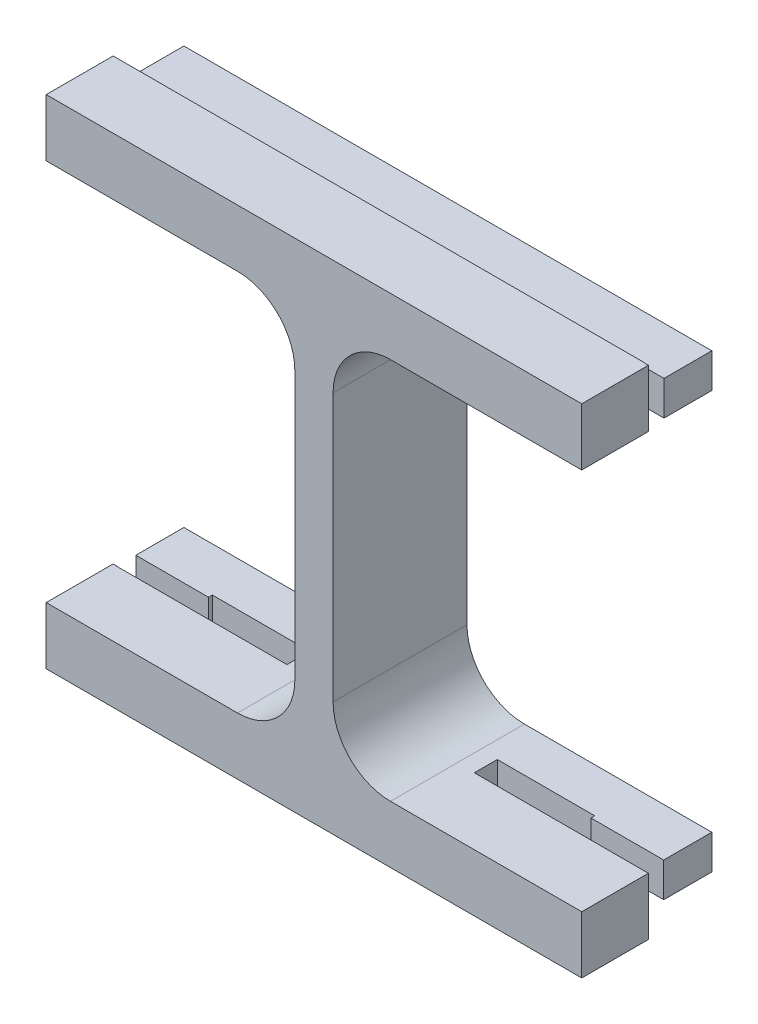
SolidWorks part; units mm, degrees
ref_plane "Ön Düzlem" through (0, 0, 0) normal (0, 0, 1) x (1, 0, 0)
ref_plane "Üst Düzlem" through (0, 0, 0) normal (0, 1, 0) x (1, 0, 0)
ref_plane "Sağ Düzlem" through (0, 0, 0) normal (1, 0, 0) x (0, 0, -1)
sketch "Sketch1" plane through (0, 0, 0) normal (0, 0, 1) x (1, 0, 0)
  line L1 (-13.4459, 11.7857) -> (16.5541, 11.7857)
  line L2 (-13.4459, 11.7857) -> (-13.4459, -10.2143)
  line L3 (-13.4459, -10.2143) -> (16.5541, -10.2143)
  line L4 (16.5541, 11.7857) -> (16.5541, -10.2143)
  dimension "D1" = 30
  dimension "D2" = 22
extrude "Boss-Extrude1" add sketch "Sketch1" along normal blind 2
sketch "Sketch2" plane through (0, 0, 2) normal (0, 0, 1) x (1, 0, 0)
  line L0 (-13.4459, -10.2143) -> (16.5541, -10.2143) construction
  line L1 (-12.4459, 10.7857) -> (0.5541, 10.7857)
  line L2 (-12.4459, 10.7857) -> (-12.4459, -9.2143)
  line L3 (-12.4459, -9.2143) -> (0.5541, -9.2143)
  line L4 (0.5541, 10.7857) -> (0.5541, -9.2143)
  line L5 (-13.4459, 11.7857) -> (-13.4459, -10.2143) construction
  line L6 (16.5541, -10.2143) -> (16.5541, 11.7857) construction
  line L7 (15.5541, 10.7857) -> (2.5541, 10.7857)
  line L8 (15.5541, 10.7857) -> (15.5541, -9.2143)
  line L9 (15.5541, -9.2143) -> (2.5541, -9.2143)
  line L10 (2.5541, 10.7857) -> (2.5541, -9.2143)
  dimension "D1" = 20
  dimension "D2" = 13
  dimension "D3" = 1
  dimension "D4" = 1
  dimension "D5" = 13
  dimension "D6" = 1
extrude "Cut-Extrude1" cut sketch "Sketch2" against normal blind 2
fillet "Fillet1" radius 3 8 edges at (15.5541, 10.7857, 1) (15.5541, -9.2143, 1) (2.5541, 10.7857, 1) (2.5541, -9.2143, 1) (0.5541, -9.2143, 1) (-12.4459, 10.7857, 1) (-12.4459, -9.2143, 1) (0.5541, 10.7857, 1)
sketch "Sketch3" plane through (0, 0, 0) normal (0, 0, -1) x (-1, 0, 0)
  line L1 (-16.5541, -10.2143) -> (13.4459, -10.2143)
  line L2 (-16.5541, -10.2143) -> (-16.5541, 11.7857)
  line L3 (-16.5541, 11.7857) -> (13.4459, 11.7857)
  line L4 (13.4459, -10.2143) -> (13.4459, 11.7857)
extrude "Boss-Extrude2" add sketch "Sketch3" along normal blind 20
sketch "Sketch4" plane through (0, 11.7857, 0) normal (0, 1, 0) x (1, 0, 0)
  line L1 (-13.4459, -2) -> (16.5541, -2)
  line L2 (-13.4459, -2) -> (-13.4459, 20)
  line L3 (-13.4459, 20) -> (16.5541, 20)
  line L4 (16.5541, -2) -> (16.5541, 20)
extrude "Boss-Extrude3" add sketch "Sketch4" along normal blind 2
sketch "Sketch5" plane through (0, -10.2143, 0) normal (0, -1, 0) x (-1, 0, 0)
  line L1 (-16.5541, -2) -> (13.4459, -2)
  line L2 (-16.5541, -2) -> (-16.5541, 20)
  line L3 (-16.5541, 20) -> (13.4459, 20)
  line L4 (13.4459, -2) -> (13.4459, 20)
extrude "Boss-Extrude4" add sketch "Sketch5" along normal blind 2
sketch "Sketch6" plane through (16.5541, 0, 0) normal (1, 0, 0) x (0, 0, -1)
  line L0 (20, -12.2143) -> (-2, -12.2143) construction
  line L1 (20, 13.7857) -> (1.9849, 13.7857)
  line L2 (20, 13.7857) -> (20, -12.2143)
  line L3 (20, -12.2143) -> (1.9849, -12.2143)
  line L4 (1.9849, 13.7857) -> (1.9849, -12.2143)
extrude "Cut-Extrude2" cut sketch "Sketch6" against normal blind 1.2
sketch "Sketch7" plane through (-13.4459, 0, 0) normal (-1, 0, 0) x (0, 0, 1)
  line L0 (2, -12.2143) -> (-20, -12.2143) construction
  line L1 (-20, 13.7857) -> (-2, 13.7857)
  line L2 (-20, 13.7857) -> (-20, -12.2143)
  line L3 (-20, -12.2143) -> (-2, -12.2143)
  line L4 (-2, 13.7857) -> (-2, -12.2143)
  dimension "D1" = 4
extrude "Cut-Extrude3" cut sketch "Sketch7" against normal blind 1.2
sketch "Sketch8" plane through (0, 13.7857, 0) normal (0, 1, 0) x (1, 0, 0)
  line L1 (-12.2459, 2) -> (15.3541, 2)
  line L2 (-12.2459, 2) -> (-12.2459, 20)
  line L3 (-12.2459, 20) -> (15.3541, 20)
  line L4 (15.3541, 2) -> (15.3541, 20)
extrude "Cut-Extrude4" cut sketch "Sketch8" against normal blind 1.2
sketch "Sketch9" plane through (0, -12.2143, 0) normal (0, -1, 0) x (1, 0, 0)
  line L1 (15.3541, -1.9849) -> (-12.2459, -1.9849)
  line L2 (15.3541, -1.9849) -> (15.3541, -20)
  line L3 (15.3541, -20) -> (-12.2459, -20)
  line L4 (-12.2459, -1.9849) -> (-12.2459, -20)
extrude "Cut-Extrude5" cut sketch "Sketch9" against normal blind 1.2
sketch "Sketch10" plane through (0, 12.5857, 0) normal (0, 1, 0) x (1, 0, 0)
  line L0 (-2.4459, -2) -> (-9.4459, -2) construction
  line L1 (-12.2459, 2) -> (-3.3459, 2)
  line L2 (-12.2459, 2) -> (-12.2459, 3)
  line L3 (-12.2459, 3) -> (-3.3459, 3)
  line L4 (-3.3459, 2) -> (-3.3459, 3)
  line L5 (15.3541, 2) -> (6.4541, 2)
  line L6 (15.3541, 2) -> (15.3541, 3)
  line L7 (15.3541, 3) -> (6.4541, 3)
  line L8 (6.4541, 2) -> (6.4541, 3)
  line L9 (12.5541, -2) -> (5.5541, -2) construction
  point P10 (-5.9459, -2)
  point P13 (-5.9459, -2)
  point P14 (9.0541, -2)
  dimension "D1" = 1
  dimension "D2" = 2.6
  dimension "D3" = 2.6
extrude "Cut-Extrude7" cut sketch "Sketch10" against normal up to surface (1.8 mm away) up to face at (-5.9459, 10.7857, 1)
sketch "Sketch12" plane through (0, 12.5857, 0) normal (0, 1, 0) x (1, 0, 0)
  line L1 (-3.3459, 2) -> (-8.5459, 2)
  line L2 (-3.3459, 2) -> (-3.3459, 3.2)
  line L3 (-3.3459, 3.2) -> (-8.5459, 3.2)
  line L4 (-8.5459, 2) -> (-8.5459, 3.2)
  line L5 (6.4541, 2) -> (11.6541, 2)
  line L6 (6.4541, 2) -> (6.4541, 3.2)
  line L7 (6.4541, 3.2) -> (11.6541, 3.2)
  line L8 (11.6541, 2) -> (11.6541, 3.2)
  dimension "D1" = 5.2
  dimension "D2" = 1.2
  dimension "D3" = 5.2
extrude "Cut-Extrude8" cut sketch "Sketch12" against normal up to surface (1.8 mm away) up to face at (-7.7959, 10.7857, -2.5)
sketch "Sketch13" plane through (0, 0, 0) normal (0, 0, 1) x (1, 0, 0)
  line L0 (-9.4459, 10.7857) -> (-2.4459, 10.7857)
  line L1 (-12.4459, 7.7857) -> (-12.4459, -6.2143)
  line L2 (-9.4459, -9.2143) -> (-2.4459, -9.2143)
  line L3 (0.5541, -6.2143) -> (0.5541, 7.7857)
  line L4 (5.5541, 10.7857) -> (12.5541, 10.7857)
  line L5 (2.5541, 7.7857) -> (2.5541, -6.2143)
  line L6 (5.5541, -9.2143) -> (12.5541, -9.2143)
  line L7 (15.5541, -6.2143) -> (15.5541, 7.7857)
  arc A0 (-9.4459, 10.7857) -> (-12.4459, 7.7857) centre (-9.4459, 7.7857) ccw
  arc A1 (-12.4459, -6.2143) -> (-9.4459, -9.2143) centre (-9.4459, -6.2143) ccw
  arc A2 (-2.4459, -9.2143) -> (0.5541, -6.2143) centre (-2.4459, -6.2143) ccw
  arc A3 (0.5541, 7.7857) -> (-2.4459, 10.7857) centre (-2.4459, 7.7857) ccw
  arc A4 (5.5541, 10.7857) -> (2.5541, 7.7857) centre (5.5541, 7.7857) ccw
  arc A5 (2.5541, -6.2143) -> (5.5541, -9.2143) centre (5.5541, -6.2143) ccw
  arc A6 (12.5541, -9.2143) -> (15.5541, -6.2143) centre (12.5541, -6.2143) ccw
  arc A7 (15.5541, 7.7857) -> (12.5541, 10.7857) centre (12.5541, 7.7857) ccw
extrude "Cut-Extrude9" cut sketch "Sketch13" against normal up to surface (3.2 mm away) up to face at (-5.9459, 11.6857, -3.2)
sketch "Sketch14" plane through (0, 10.7857, 0) normal (0, 1, 0) x (1, 0, 0)
  line L1 (12.5541, 2) -> (15.3541, 2)
  line L2 (12.5541, 2) -> (12.5541, 3)
  line L3 (12.5541, 3) -> (15.3541, 3)
  line L4 (15.3541, 2) -> (15.3541, 3)
  line L5 (-12.2459, 3) -> (-9.4459, 3)
  line L6 (-12.2459, 3) -> (-12.2459, 2)
  line L7 (-12.2459, 2) -> (-9.4459, 2)
  line L8 (-9.4459, 3) -> (-9.4459, 2)
extrude "Cut-Extrude10" cut sketch "Sketch14" against normal blind 5
sketch "Sketch15" plane through (0, -11.0143, 0) normal (0, -1, 0) x (-1, 0, 0)
  line L0 (9.4459, -2) -> (2.4459, -2) construction
  line L1 (12.2459, 1.9849) -> (3.3459, 1.9849)
  line L2 (12.2459, 1.9849) -> (12.2459, 2.9849)
  line L3 (12.2459, 2.9849) -> (3.3459, 2.9849)
  line L4 (3.3459, 1.9849) -> (3.3459, 2.9849)
  line L5 (-15.3541, 1.9849) -> (-6.4541, 1.9849)
  line L6 (-15.3541, 1.9849) -> (-15.3541, 2.9849)
  line L7 (-15.3541, 2.9849) -> (-6.4541, 2.9849)
  line L8 (-6.4541, 1.9849) -> (-6.4541, 2.9849)
  line L9 (-5.5541, -2) -> (-12.5541, -2) construction
  point P10 (5.9459, -2)
  point P13 (-9.0541, -2)
  dimension "D1" = 2.6
  dimension "D2" = 2.6
  dimension "D3" = 1
  dimension "D4" = 1
extrude "Cut-Extrude11" cut sketch "Sketch15" against normal blind 5
sketch "Sketch16" plane through (0, -11.0143, 0) normal (0, -1, 0) x (-1, 0, 0)
  line L1 (3.3459, 1.9849) -> (8.4459, 1.9849)
  line L2 (3.3459, 1.9849) -> (3.3459, 3.1849)
  line L3 (3.3459, 3.1849) -> (8.4459, 3.1849)
  line L4 (8.4459, 1.9849) -> (8.4459, 3.1849)
  line L5 (-6.4541, 1.9849) -> (-11.5541, 1.9849)
  line L6 (-6.4541, 1.9849) -> (-6.4541, 3.1849)
  line L7 (-6.4541, 3.1849) -> (-11.5541, 3.1849)
  line L8 (-11.5541, 1.9849) -> (-11.5541, 3.1849)
  dimension "D1" = 5.1
  dimension "D2" = 5.1
  dimension "D3" = 1.2
  dimension "D4" = 1.2
extrude "Cut-Extrude12" cut sketch "Sketch16" against normal blind 5
sketch "Sketch17" plane through (0, 12.5857, 0) normal (0, 1, 0) x (1, 0, 0)
  line L0 (-12.2459, 20) -> (-12.2459, 3) construction
  line L1 (-12.2459, 5.5) -> (15.3541, 5.5)
  line L2 (-12.2459, 5.5) -> (-12.2459, 20)
  line L3 (-12.2459, 20) -> (15.3541, 20)
  line L4 (15.3541, 5.5) -> (15.3541, 20)
  dimension "D1" = 2.5
extrude "Cut-Extrude13" cut sketch "Sketch17" against normal up to surface (23.6 mm away) up to face at (1.5541, -11.0143, -5.7207)
sketch "Sketch18" plane through (0, 0, -3.2) normal (0, 0, 1) x (1, 0, 0)
  line L0 (-12.4459, 7.7857) -> (-12.4459, -6.2143)
  line L2 (-9.4459, -9.2143) -> (-2.4459, -9.2143)
  line L4 (0.5541, -6.2143) -> (0.5541, 7.7857)
  line L6 (-2.4459, 10.7857) -> (-9.4459, 10.7857)
  line L8 (5.5541, 10.7857) -> (12.5541, 10.7857)
  line L10 (15.5541, 7.7857) -> (15.5541, -6.2143)
  line L12 (12.5541, -9.2143) -> (5.5541, -9.2143)
  line L14 (2.5541, -6.2143) -> (2.5541, 7.7857)
  arc A0 (-9.4459, 10.7857) -> (-12.4459, 7.7857) centre (-9.4459, 7.7857) ccw
  arc A1 (0.5541, 7.7857) -> (-2.4459, 10.7857) centre (-2.4459, 7.7857) ccw
  arc A2 (5.5541, 10.7857) -> (2.5541, 7.7857) centre (5.5541, 7.7857) ccw
  arc A3 (12.5541, -9.2143) -> (15.5541, -6.2143) centre (12.5541, -6.2143) ccw
  arc A4 (15.5541, 7.7857) -> (12.5541, 10.7857) centre (12.5541, 7.7857) ccw
  arc A5 (2.5541, -6.2143) -> (5.5541, -9.2143) centre (5.5541, -6.2143) ccw
  arc A6 (-2.4459, -9.2143) -> (0.5541, -6.2143) centre (-2.4459, -6.2143) ccw
  arc A7 (-12.4459, -6.2143) -> (-9.4459, -9.2143) centre (-9.4459, -6.2143) ccw
extrude "Cut-Extrude14" cut sketch "Sketch18" against normal blind 5
sketch "Sketch19" plane through (0, 0, -5.5) normal (0, 0, -1) x (-1, 0, 0)
  line L2 (-15.3541, 10.7857) -> (-15.3541, -9.2143)
  line L4 (-12.5541, 10.7857) -> (-12.5541, -9.2143)
  line L7 (12.2459, -9.2143) -> (12.2459, 10.7857)
  line L9 (9.4459, -9.2143) -> (9.4459, 10.7857)
  line L10 (-12.5541, 10.7857) -> (-15.3541, 10.7857)
  line L11 (-12.5541, -9.2143) -> (-15.3541, -9.2143)
  line L12 (9.4459, 10.7857) -> (12.2459, 10.7857)
  line L13 (9.4459, -9.2143) -> (12.2459, -9.2143)
extrude "Cut-Extrude16" cut sketch "Sketch19" against normal up to surface (3.5 mm away) up to face at (-2.6154, 5.4033, -2)
sketch "Sketch20" plane through (0, 0, 2) normal (0, 0, 1) x (1, 0, 0)
  line L1 (-9.4459, 10.7857) -> (-18.0208, 10.7857)
  line L2 (-9.4459, 10.7857) -> (-9.4459, -9.2143)
  line L3 (-9.4459, -9.2143) -> (-18.0208, -9.2143)
  line L4 (-18.0208, 10.7857) -> (-18.0208, -9.2143)
  line L5 (-13.4459, 13.7857) -> (-13.4459, -12.2143) construction
  line L6 (12.5541, -9.2143) -> (25.1682, -9.2143)
  line L7 (12.5541, -9.2143) -> (12.5541, 10.7857)
  line L8 (12.5541, 10.7857) -> (25.1682, 10.7857)
  line L9 (25.1682, -9.2143) -> (25.1682, 10.7857)
  dimension "D1" = 0
extrude "Cut-Extrude18" cut sketch "Sketch20" against normal blind 5
sketch "Sketch24" plane through (-13.4459, 0, 0) normal (-1, 0, 0) x (0, 0, 1)
  line L0 (-1.9849, -12.2143) -> (2, -12.2143) construction
  line L1 (2, 13.7857) -> (1.5, 13.7857)
  line L2 (2, 13.7857) -> (2, -12.2143)
  line L3 (2, -12.2143) -> (1.5, -12.2143)
  line L4 (1.5, 13.7857) -> (1.5, -12.2143)
  dimension "D1" = 0.5
extrude "Cut-Extrude19" cut sketch "Sketch24" against normal blind 100
sketch "Sketch25" plane through (0, 0, 1.5) normal (0, 0, 1) x (1, 0, 0)
  line L1 (-16.5888, 15.5187) -> (-12.4459, 15.5187)
  line L2 (-16.5888, 15.5187) -> (-16.5888, -13.0151)
  line L3 (-16.5888, -13.0151) -> (-12.4459, -13.0151)
  line L4 (-12.4459, 15.5187) -> (-12.4459, -13.0151)
  line L5 (20.0076, -13.6365) -> (15.5541, -13.6365)
  line L6 (20.0076, -13.6365) -> (20.0076, 15.5187)
  line L7 (20.0076, 15.5187) -> (15.5541, 15.5187)
  line L8 (15.5541, -13.6365) -> (15.5541, 15.5187)
  dimension "D1" = 1
  dimension "D2" = 1
extrude "Cut-Extrude20" cut sketch "Sketch25" against normal blind 3.5
